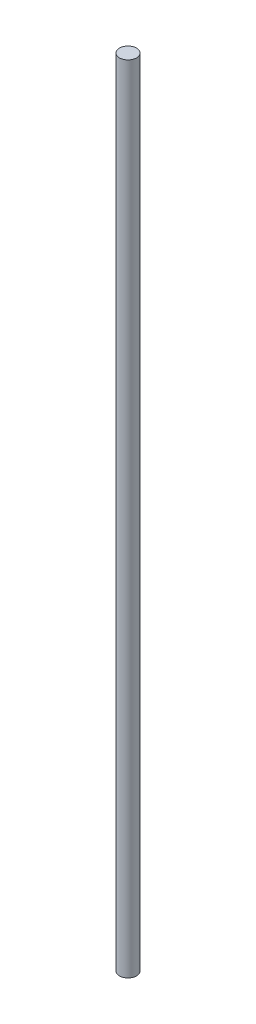
SolidWorks part; units mm, degrees
material "6061-T6 (SS)"
ref_plane "Front Plane" through (0, 0, 0) normal (0, 0, 1) x (1, 0, 0)
ref_plane "Top Plane" through (0, 0, 0) normal (0, 1, 0) x (1, 0, 0)
ref_plane "Right Plane" through (0, 0, 0) normal (1, 0, 0) x (0, 0, -1)
sketch "Sketch1" plane through (0, 0, 0) normal (0, 1, 0) x (1, 0, 0)
  circle A0 centre (0, 0) radius 3
  dimension "D1" = 6
extrude "Boss-Extrude1" add sketch "Sketch1" along normal mid plane 279.4
